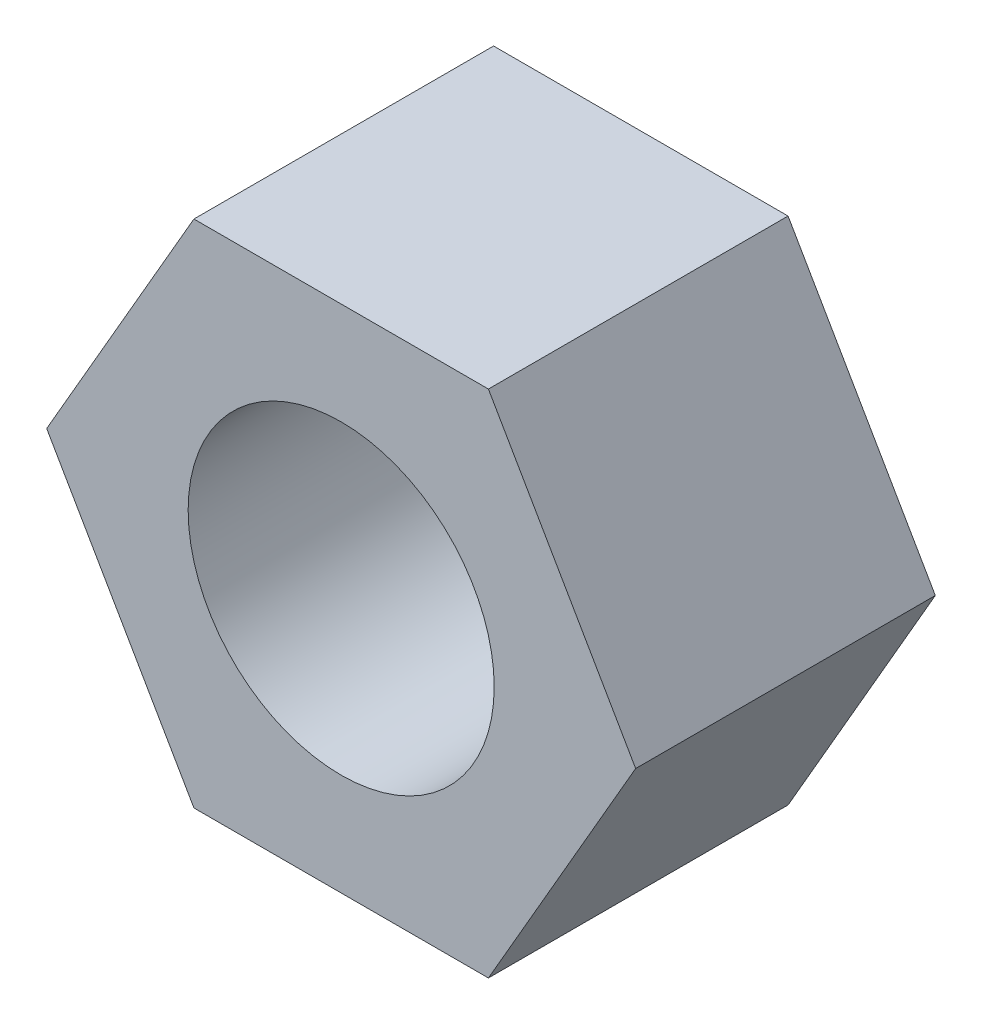
SolidWorks part; units mm, degrees
ref_plane "Front Plane" through (0, 0, 0) normal (0, 0, 1) x (1, 0, 0)
ref_plane "Top Plane" through (0, 0, 0) normal (0, 1, 0) x (1, 0, 0)
ref_plane "Right Plane" through (0, 0, 0) normal (1, 0, 0) x (0, 0, -1)
sketch "Sketch1" plane through (0, 0, 0) normal (0, 0, 1) x (1, 0, 0)
  line L1 (4.6188, 0) -> (2.3094, 4)
  line L2 (2.3094, 4) -> (-2.3094, 4)
  line L3 (-2.3094, 4) -> (-4.6188, 0)
  line L4 (-4.6188, 0) -> (-2.3094, -4)
  line L5 (-2.3094, -4) -> (2.3094, -4)
  line L6 (2.3094, -4) -> (4.6188, 0)
  circle A0 centre (0, 0) radius 4 construction
  dimension "D1" = 8
extrude "Boss-Extrude1" add sketch "Sketch1" along normal mid plane 4.7
sketch "Sketch2" plane through (0, 0, 2.35) normal (0, 0, 1) x (1, 0, 0)
  circle A0 centre (0, 0) radius 2.4
  dimension "D1" = 4.8
extrude "Cut-Extrude1" cut sketch "Sketch2" against normal through all
